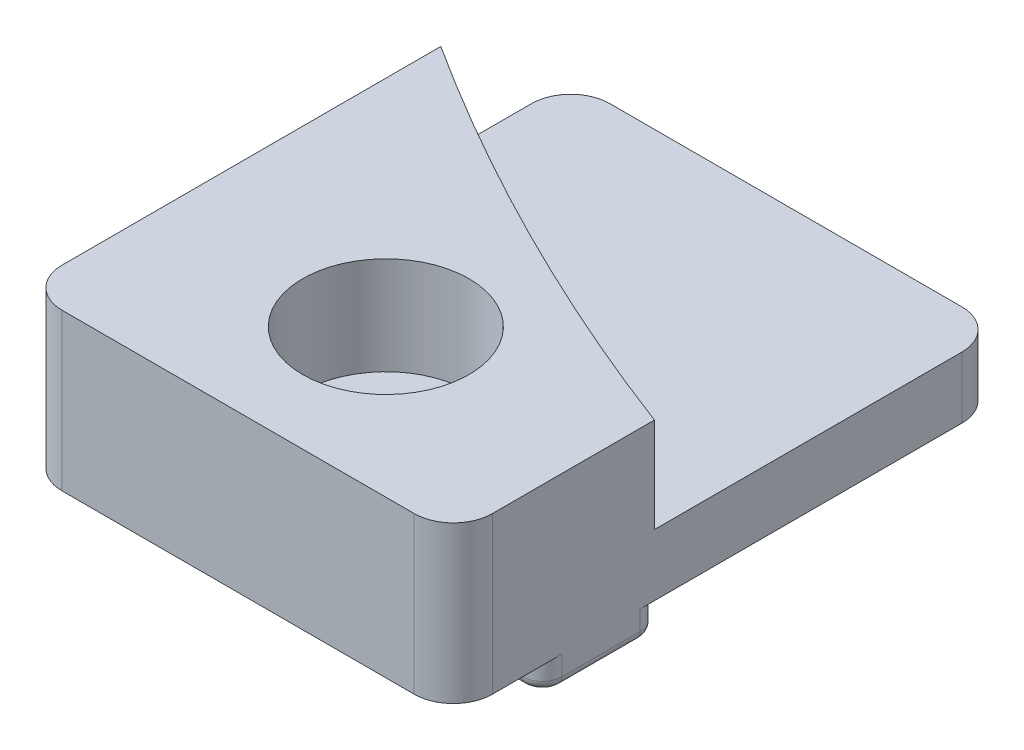
SolidWorks part; units mm, degrees
ref_plane "Front Plane" through (0, 0, 0) normal (0, 0, 1) x (1, 0, 0)
ref_plane "Top Plane" through (0, 0, 0) normal (0, 1, 0) x (1, 0, 0)
ref_plane "Right Plane" through (0, 0, 0) normal (1, 0, 0) x (0, 0, -1)
ref_plane "Plane1" through (0, 8, 0) normal (0, 1, 0) x (1, 0, 0)
sketch "Sketch1" plane through (0, 8, 0) normal (0, 1, 0) x (1, 0, 0)
  line L0 (-11, 14) -> (-11, -14)
  line L1 (-11, -14) -> (11, -14)
  line L2 (11, -14) -> (11, 14)
  line L3 (11, 14) -> (-11, 14)
extrude "Boss-Extrude1" add sketch "Sketch1" against normal blind 9.5
sketch "Sketch2" plane through (-11, 0, 0) normal (-1, 0, 0) x (0, 0, 1)
  line L0 (3.45, -1.5) -> (3.45, 0)
  line L1 (3.45, 0) -> (-14, 0)
  line L2 (-14, 0) -> (-14, -1.5)
  line L3 (-14, -1.5) -> (3.45, -1.5)
extrude "Cut-Extrude1" cut sketch "Sketch2" against normal through all
sketch "Sketch3" plane through (0, 8, 0) normal (0, 1, 0) x (-1, 0, 0)
  line L0 (11, -14) -> (11, -7.3586)
  line L1 (-11, 3.7188) -> (-11, -14)
  line L2 (-11, -14) -> (11, -14)
  arc A0 (11, -7.3586) -> (-11, 3.7188) centre (-53.23, -107.536) ccw
extrude "Cut-Extrude2" cut sketch "Sketch3" against normal blind 4.85
sketch "Sketch4" plane through (-11, 0, 0) normal (-1, 0, 0) x (0, 0, 1)
  line L0 (14, -1.5) -> (14, 0)
  line L1 (14, 0) -> (9.45, 0)
  line L2 (9.45, 0) -> (9.45, -1.5)
  line L3 (9.45, -1.5) -> (14, -1.5)
extrude "Cut-Extrude3" cut sketch "Sketch4" against normal through all
hole_wizard "CBORE for M4 Hex Head Machine Screw1" positions "Sketch6" profile "Sketch5" counterbore size "M4" standard "ANSI Metric"
sketch "Sketch6" plane through (0, 8, 0) normal (0, 1, 0) x (1, 0, 0)
  point P0 (0, -6.45)
sketch "Sketch5" plane through (0, 8, 6.45) normal (1, 0, 0) x (0, 0, 1)
  line L0 (0, 0) -> (0, 9.5)
  line L1 (0, 9.5) -> (2.15, 9.5)
  line L3 (2.15, 9.5) -> (2.15, 5)
  line L4 (2.15, 5) -> (4.25, 5)
  line L5 (4.25, 5) -> (4.25, 0)
  line L7 (4.25, 0) -> (0, 0)
  line L11 (0, -6.35) -> (0, 107.95) construction
  dimension "Thru Hole Dia." = 4.3
  dimension "Thru Hole Depth" = 9.5
  dimension "C'Bore Dia." = 8.5
  dimension "C'Bore Depth" = 5
fillet "Fillet1" radius 1 4 edges at (-11, -0.75, 3.45) (11, -0.75, 3.45) (-11, -0.75, 9.45) (11, -0.75, 9.45)
fillet "Fillet2" radius 0.5 8 edges at (-10.7071, -1.5, 3.7429) (-11, -1.5, 6.45) (0, -1.5, 3.45) (-10.7071, -1.5, 9.1571) (10.7071, -1.5, 3.7429) (0, -1.5, 9.45) (11, -1.5, 6.45) (10.7071, -1.5, 9.1571)
fillet "Fillet3" radius 2 4 edges at (11, 1.575, -14) (-11, 1.575, -14) (11, 4, 14) (-11, 4, 14)
